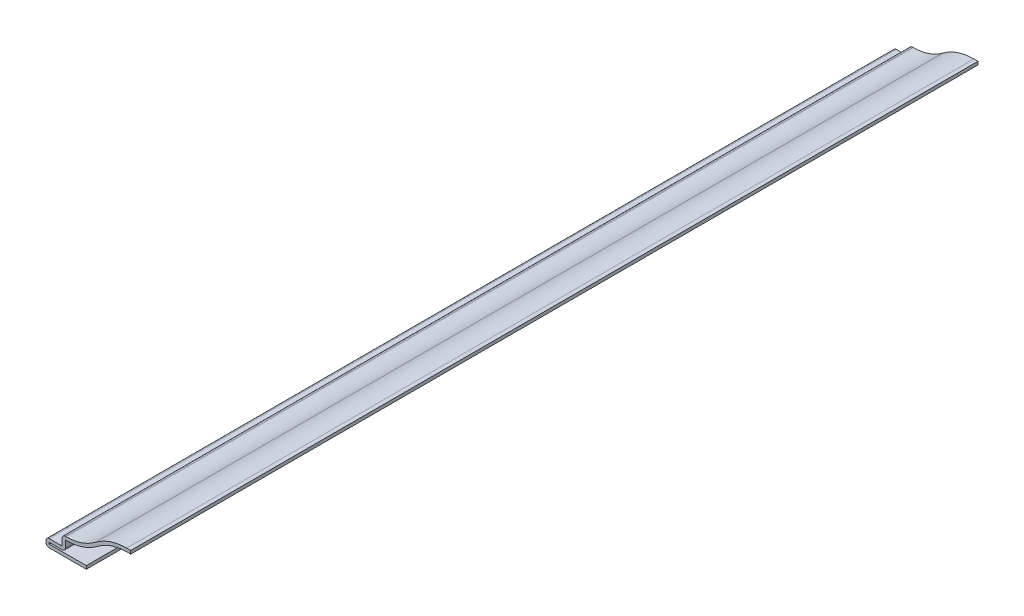
SolidWorks part; units mm, degrees
ref_plane "Front Plane" through (0, 0, 0) normal (0, 0, 1) x (1, 0, 0)
ref_plane "Top Plane" through (0, 0, 0) normal (0, 1, 0) x (1, 0, 0)
ref_plane "Right Plane" through (0, 0, 0) normal (1, 0, 0) x (0, 0, -1)
sketch "Sketch1" plane through (0, 0, 0) normal (0, 0, 1) x (1, 0, 0)
  line L0 (0, 0) -> (0, 15.1606) construction
  line L1 (-26.9875, 7.1225) -> (-26.9875, 3.175)
  line L2 (-26.9875, 3.175) -> (-33.3375, 3.175)
  line L3 (-33.3375, 3.175) -> (-33.3375, 0)
  line L4 (-33.3375, 0) -> (-17.4625, 0)
  line L5 (0, 15.1606) -> (19.6983, 15.1606) construction
  line L6 (-26.9875, 7.1225) -> (-25.4, 7.1225)
  line L7 (0, 15.1606) -> (-1.5875, 15.1606)
  line L8 (0, 13.8906) -> (-1.5875, 13.8906) construction
  arc A0 (-1.5875, 15.1606) -> (-13.8545, 11.0198) centre (-1.5875, -5.08) ccw
  arc A1 (-25.4, 7.1225) -> (-13.8545, 11.0198) centre (-25.4, 26.1725) ccw
  point P13 (0, 0)
  point P14 (0, 0)
  point P18 (0, 0)
  dimension "D6" = 19.05
  dimension "D8" = 20.2406
  dimension "D2" = 3.175
  dimension "D3" = 6.35
  dimension "D4" = 15.875
  dimension "D5" = 1.5875
  dimension "D7" = 1.5875
  dimension "D9" = 26.9875
  dimension "D10" = 1.27
  dimension "D11" = 33.3375
  dimension "D12" = 13.8906
extrude "Extrude-Thin1" add sketch "Sketch1" against normal blind 333.375 thin thin type one direction reverse wall 1.27
fillet "Fillet1" radius 1.27 4 edges at (-25.7175, 1.905, -166.6875) (-33.3375, 0, -166.6875) (-33.3375, 3.175, -166.6875) (-26.9875, 7.1225, -166.6875)
